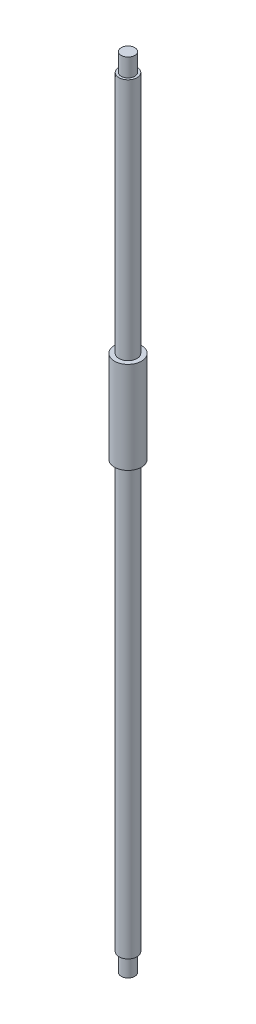
SolidWorks part; units mm, degrees
material "AISI 1020"
ref_plane "Front Plane" through (0, 0, 0) normal (0, 0, 1) x (1, 0, 0)
ref_plane "Top Plane" through (0, 0, 0) normal (0, 1, 0) x (1, 0, 0)
ref_plane "Right Plane" through (0, 0, 0) normal (1, 0, 0) x (0, 0, -1)
sketch "Sketch1" plane through (0, 0, 0) normal (0, 1, 0) x (1, 0, 0)
  circle A0 centre (0, 0) radius 12.7
  dimension "D1" = 25.4
extrude "Boss-Extrude1" add sketch "Sketch1" along normal blind 1120
sketch "Sketch3" plane through (0, 0, 0) normal (0, -1, 0) x (1, 0, 0)
  circle A0 centre (0, 0) radius 12.7
  circle A1 centre (0, 0) radius 9.525
  dimension "D1" = 19.05
extrude "Cut-Extrude1" cut sketch "Sketch3" against normal blind 25.4
sketch "Sketch4" plane through (0, 1120, 0) normal (0, 1, 0) x (1, 0, 0)
  circle A0 centre (0, 0) radius 12.7
  circle A1 centre (0, 0) radius 9.525
  circle M3 centre (0, 0) radius 12.7
  dimension "D1" = 19.05
extrude "Cut-Extrude2" cut sketch "Sketch4" against normal blind 25.4 contours A1 M3 | A0
ref_plane "Plane1" through (0, 560, 0) normal (0, 1, 0) x (1, 0, 0)
ref_plane "Plane2" through (0, 753, 0) normal (0, 1, 0) x (1, 0, 0)
sketch "Sketch5" plane through (0, 753, 0) normal (0, 1, 0) x (1, 0, 0)
  circle A0 centre (0, 0) radius 12.7
  circle A1 centre (0, 0) radius 19.05
  dimension "D1" = 38.1
extrude "Boss-Extrude2" add sketch "Sketch5" against normal blind 129
